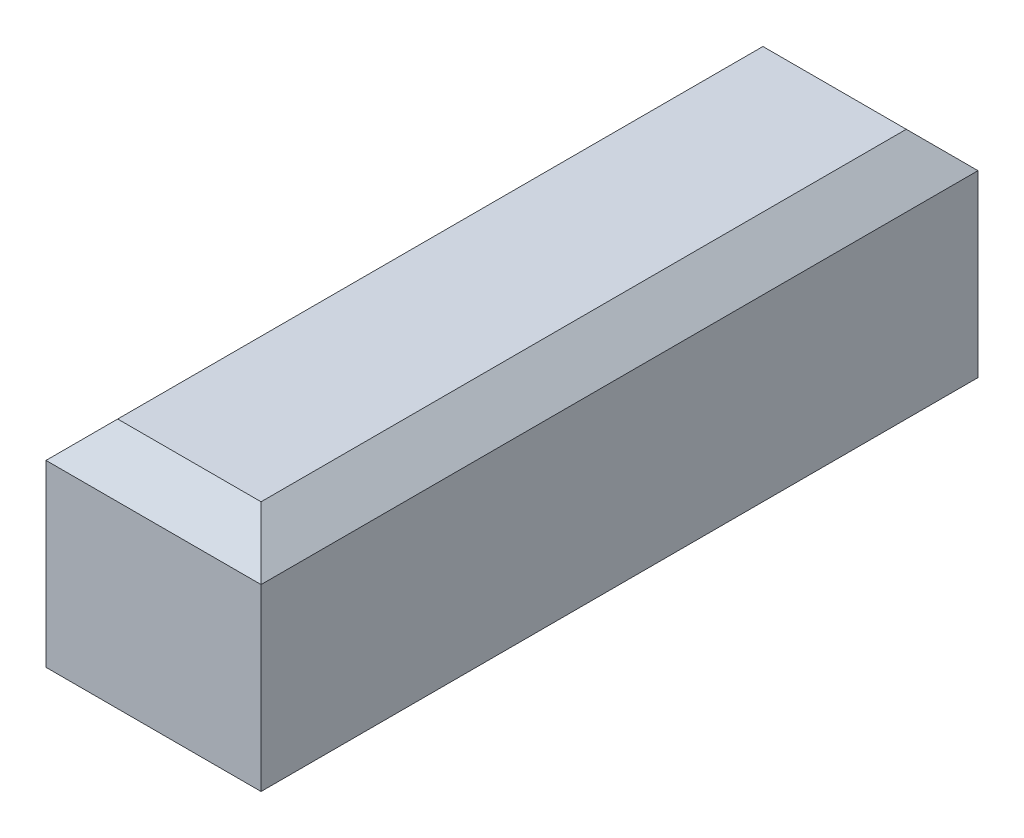
SolidWorks part; units mm, degrees
ref_plane "Front Plane" through (0, 0, 0) normal (0, 0, 1) x (1, 0, 0)
ref_plane "Top Plane" through (0, 0, 0) normal (0, 1, 0) x (1, 0, 0)
ref_plane "Right Plane" through (0, 0, 0) normal (1, 0, 0) x (0, 0, -1)
sketch "Sketch1" plane through (0, 0, 0) normal (0, 1, 0) x (1, 0, 0)
  line L1 (0, 0) -> (-18, 0)
  line L2 (0, 0) -> (0, 60)
  line L3 (0, 60) -> (-18, 60)
  line L4 (-18, 0) -> (-18, 60)
  dimension "D1" = 18
  dimension "D2" = 60
extrude "Boss-Extrude1" add sketch "Sketch1" along normal blind 18
chamfer "Chamfer1" distance 3 angle 45 4 edges at (-9, 18, -60) (0, 18, -30) (-9, 18, 0) (-18, 18, -30)
